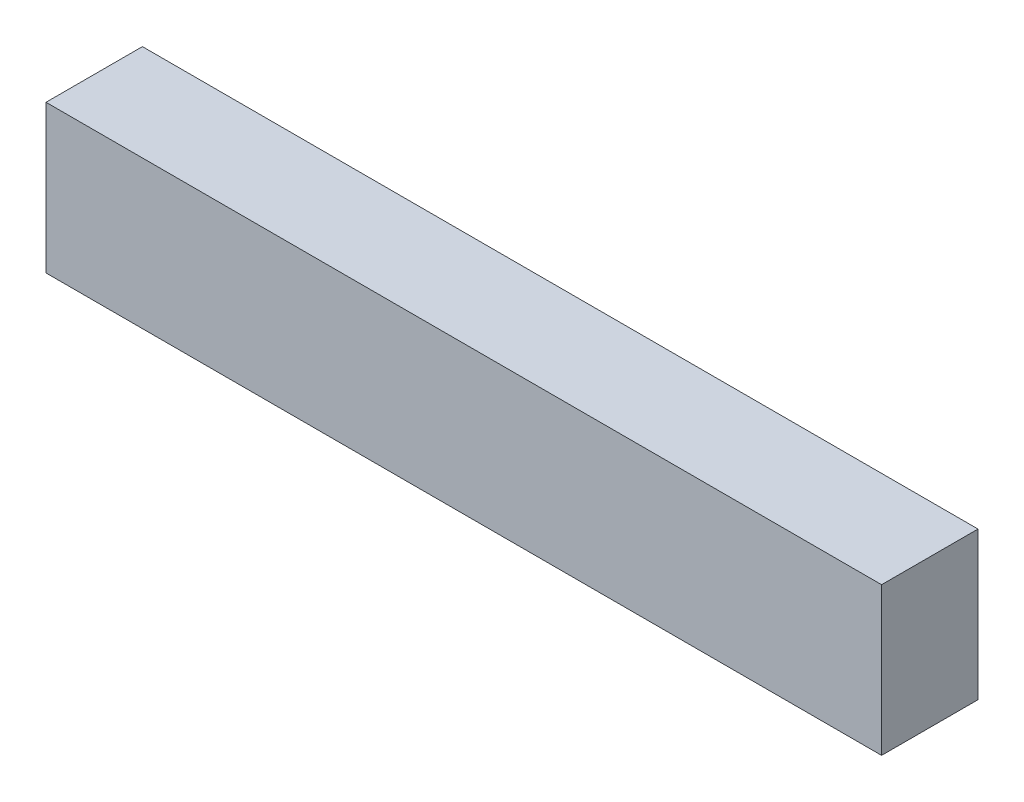
SolidWorks part; units mm, degrees
ref_plane "Front Plane" through (0, 0, 0) normal (0, 0, 1) x (1, 0, 0)
ref_plane "Top Plane" through (0, 0, 0) normal (0, 1, 0) x (1, 0, 0)
ref_plane "Right Plane" through (0, 0, 0) normal (1, 0, 0) x (0, 0, -1)
sketch "Sketch2" plane through (0, 0, 0) normal (0, 1, 0) x (1, 0, 0)
  line L1 (-65, -7.5) -> (65, -7.5)
  line L2 (-65, -7.5) -> (-65, 7.5)
  line L3 (-65, 7.5) -> (65, 7.5)
  line L4 (65, -7.5) -> (65, 7.5)
  line L5 (-65, -7.5) -> (65, 7.5) construction
  line L6 (-65, 7.5) -> (65, -7.5) construction
  point P0 (0, 0)
  dimension "D1" = 130
  dimension "D2" = 15
extrude "Boss-Extrude1" add sketch "Sketch2" along normal blind 23
